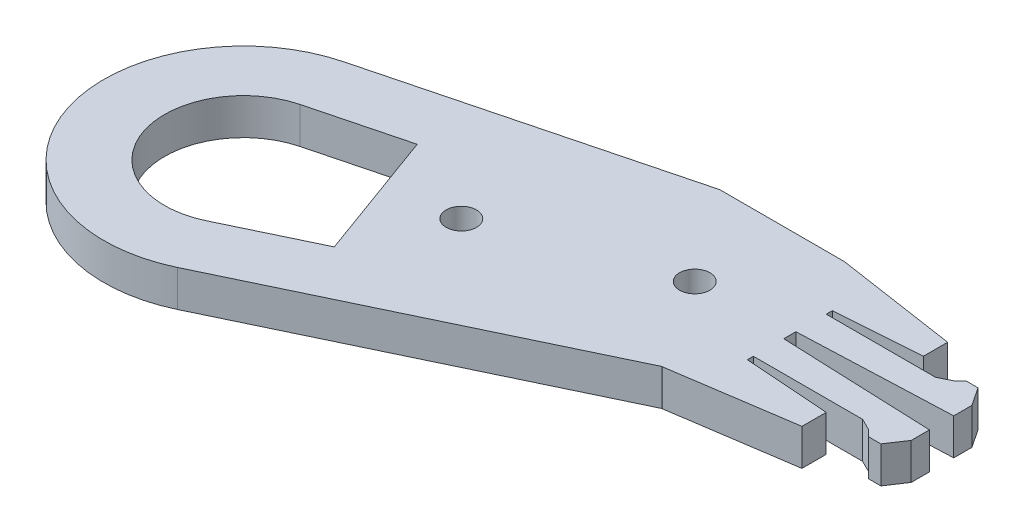
SolidWorks part; units mm, degrees
material "Lasercut ABS"
ref_plane "Front Plane" through (0, 0, 0) normal (0, 0, 1) x (1, 0, 0)
ref_plane "Top Plane" through (0, 0, 0) normal (0, 1, 0) x (1, 0, 0)
ref_plane "Right Plane" through (0, 0, 0) normal (1, 0, 0) x (0, 0, -1)
sketch "Sketch4" plane through (0, 0, 0) normal (0, 1, 0) x (1, 0, 0)
  line L0 (0, 0) -> (0, 17.2192) construction
  line L1 (-2.8794, 11.1337) -> (21.7373, 17.5)
  line L2 (4.9509, -10.3797) -> (31.9538, 2.5)
  line L3 (32, 2.5) -> (31.9538, 2.5)
  line L4 (32, 17.5) -> (21.7373, 17.5)
  arc A0 (-2.8794, 11.1337) -> (4.9509, -10.3797) centre (0, 0) ccw
  line B0 (6.0339, 8.2743) -> (9.9409, -2.46)
  line B1 (0, 0) -> (7.9874, 2.9072) construction
  line B2 (6.0339, 8.2743) -> (-1.6275, 6.293)
  line B3 (9.9409, -2.46) -> (2.7983, -5.8668)
  arc B4 (-1.6275, 6.293) -> (2.7983, -5.8668) centre (0, 0) ccw
  circle B5 centre (13.1557, 4.7883) radius 1.25
  circle B6 centre (27.2511, 9.9186) radius 1.25
  line B7 (32, 10) -> (35, 10) construction
  line B8 (35, 10.5) -> (35, 9.5)
  line B9 (35, 10.5) -> (47.5, 11)
  line B10 (47.5, 11) -> (47.5, 12.5)
  line B11 (47.5, 12.5) -> (46.5, 14)
  line B12 (46.5, 14) -> (45.5, 14)
  line B13 (45.5, 14) -> (45, 13.5)
  line B14 (45, 13.5) -> (44, 13)
  line B15 (44, 13) -> (35, 13)
  line B16 (35, 13) -> (35, 13.5)
  line B17 (35, 13.5) -> (42, 14)
  line B18 (42, 14) -> (42, 16)
  line B19 (42, 16) -> (32, 17.5)
  line B20 (35, 9.5) -> (47.5, 9)
  line B21 (47.5, 9) -> (47.5, 7.5)
  line B22 (47.5, 7.5) -> (46.5, 6)
  line B23 (46.5, 6) -> (45.5, 6)
  line B24 (45.5, 6) -> (45, 6.5)
  line B25 (45, 6.5) -> (44, 7)
  line B26 (44, 7) -> (35, 7)
  line B27 (35, 7) -> (35, 6.5)
  line B28 (35, 6.5) -> (42, 6)
  line B29 (42, 6) -> (42, 4)
  line B30 (42, 4) -> (32, 2.5)
  dimension "D1" = 70
  dimension "D2" = 5
  dimension "D3" = 10
  dimension "D4" = 42
sketch_block_instance "Block-Horn-TowerPro-1"
sketch_block "Block1" parameters "D1"=6.5, "D4"=2.5, "D2"=15, "D3"=11, "D5"=14, "D6"=15
sketch_block_instance "Block-Snap-Textile-1"
sketch_block "Block-Snap-Textile" parameters "D1"=3, "D2"=1, "D3"=2, "D4"=1.5, "D5"=10, "D6"=0.5, "D7"=9, "D8"=1, "D9"=0.5, "D10"=0.5, "D11"=0.5, "D12"=1, "D13"=12.5, "D14"=0.5, "D15"=0.5, "D16"=1.5, "D17"=1.5
extrude "Boss-Extrude2" add sketch "Sketch4" against normal blind 3 contours L0 A0 L2 L3 B30 B29 B28 B27 B26 B25 B24 B23 B22 B21 B20 B8 B9 B10 B11 B12 B13 B14 B15 B16 B17 B18 B19 L4 L1 B2 B0 B3 B4 B6 B5 | A0 L0 B4 B2 L1
sketch "Sketch5" plane through (0, 0, 0) normal (0, 1, 0) x (1, 0, 0)
  line L0 (4.6595, 12.0505) -> (20.1499, 16.0566) construction
  line L1 (10.4563, -3.876) -> (24.8976, 3.0121) construction
  line L2 (6.0339, 8.2743) -> (9.9409, -2.46) construction
  line L3 (-2.8794, 11.1337) -> (21.7373, 17.5) construction
  line L4 (4.9509, -10.3797) -> (31.9538, 2.5) construction
  text T0 "ONO V2" font "1CamBam_Stick_3" height 2.5
  text T1 "M9" font "1CamBam_Stick_3" height 2.5
  dimension "D1" = 16
  dimension "D2" = 1
  dimension "D3" = 3.5
equation "\"X\"= 10"
equation "\"Y\"= 42"
equation "\"D3@Sketch4\"=\"X\""
equation "\"D4@Sketch4\"=\"Y\""
